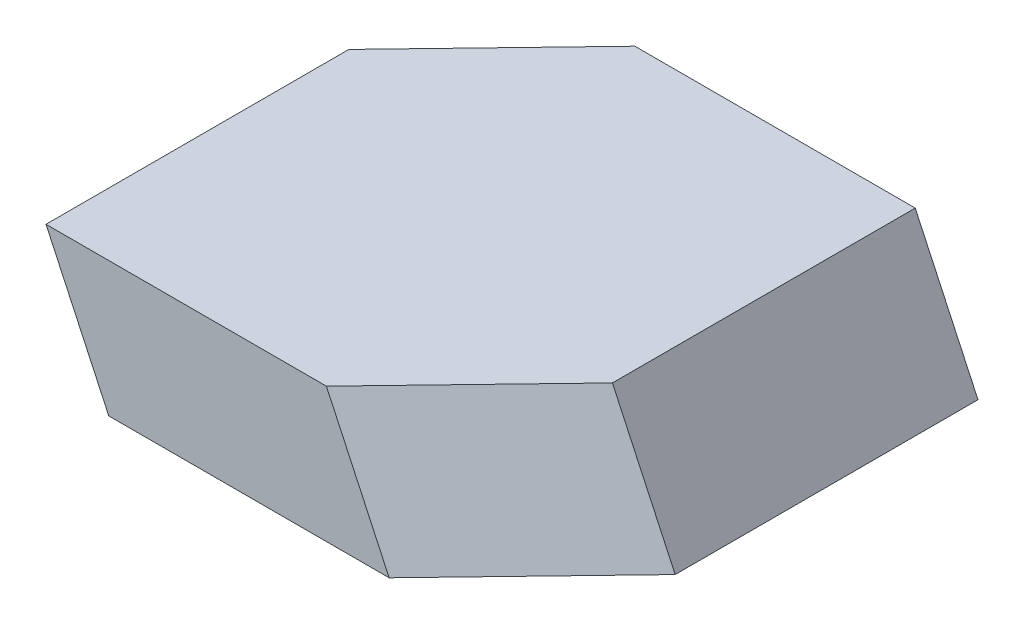
SolidWorks part; units mm, degrees
ref_plane "Front" through (0, 0, 0) normal (0, 0, 1) x (1, 0, 0)
ref_plane "Top" through (0, 0, 0) normal (0, 1, 0) x (1, 0, 0)
ref_plane "Right" through (0, 0, 0) normal (1, 0, 0) x (0, 0, -1)
sketch "Sketch1" plane through (0, 0, 0) normal (0, 1, 0) x (1, 0, 0)
  line L0 (0, 0) -> (50, 0)
  line L1 (50, 0) -> (50, -54)
  line L2 (-25, -26) -> (-25, -80)
  line L3 (-25, -80) -> (25, -80)
  line L4 (0, -80) -> (50, -80) construction
  line L5 (-25, 0) -> (-25, -54) construction
  line L6 (0, 0) -> (-25, -26)
  line L7 (25, -80) -> (50, -54)
  dimension "D1" = 50
  dimension "D2" = 54
sketch "Sketch3" plane through (0, 0, 0) normal (0, 0, 1) x (1, 0, 0)
  line L0 (50, 0) -> (38.8086, 24) construction
ref_plane "Plane2" through (0, 24, 0) normal (0, 1, 0) x (-1, 0, 0)
sketch "Sketch4" plane through (0, 24, 0) normal (0, 1, 0) x (-1, 0, 0)
  line L0 (-38.8086, 0) -> (-38.8086, 54)
  line L1 (-38.8086, 0) -> (11.1914, 0)
  line L2 (-13.8086, 80) -> (36.1914, 80)
  line L3 (36.1914, 26) -> (36.1914, 80)
  line L4 (36.1914, 0) -> (36.1914, 54) construction
  line L5 (-38.8086, 80) -> (11.1914, 80) construction
  line L6 (-13.8086, 80) -> (-38.8086, 54)
  line L7 (11.1914, 0) -> (36.1914, 26)
loft "Loft1" add profiles "Sketch1", "Sketch4"
